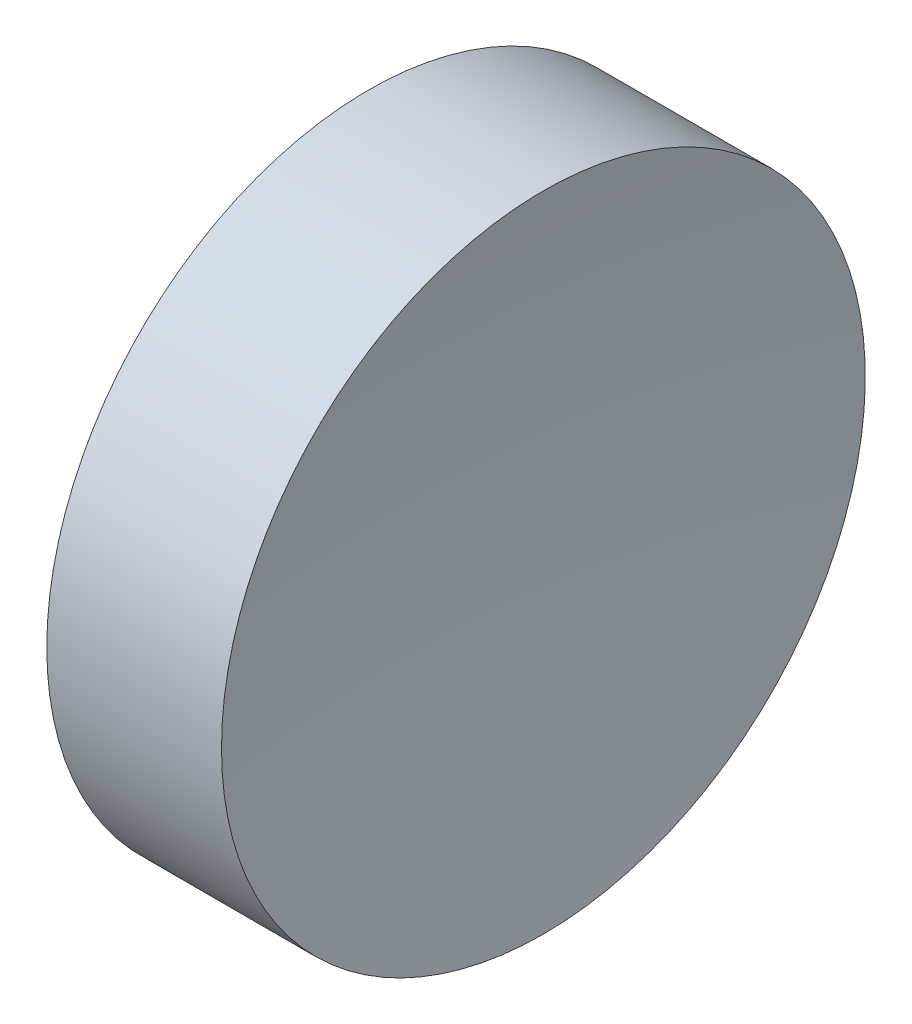
SolidWorks part; units mm, degrees
ref_plane "前视基准面" through (0, 0, 0) normal (0, 0, 1) x (1, 0, 0)
ref_plane "上视基准面" through (0, 0, 0) normal (0, 1, 0) x (1, 0, 0)
ref_plane "右视基准面" through (0, 0, 0) normal (1, 0, 0) x (0, 0, -1)
sketch "草图1" plane through (0, 0, 0) normal (0, 0, 1) x (1, 0, 0)
  line L0 (54.4926, 34.689) -> (66.3882, 34.689) construction
  line L1 (57.5463, 34.689) -> (57.5463, 40.939)
  line L2 (57.5463, 40.939) -> (60.9385, 40.939)
  line L3 (60.5463, 34.689) -> (57.5463, 34.689)
  arc A0 (60.9385, 40.939) -> (60.5463, 34.689) centre (110.5463, 34.689) ccw
  dimension "D1" = 3.3922
revolve "旋转1" add sketch "草图1" angle 360 about L0
